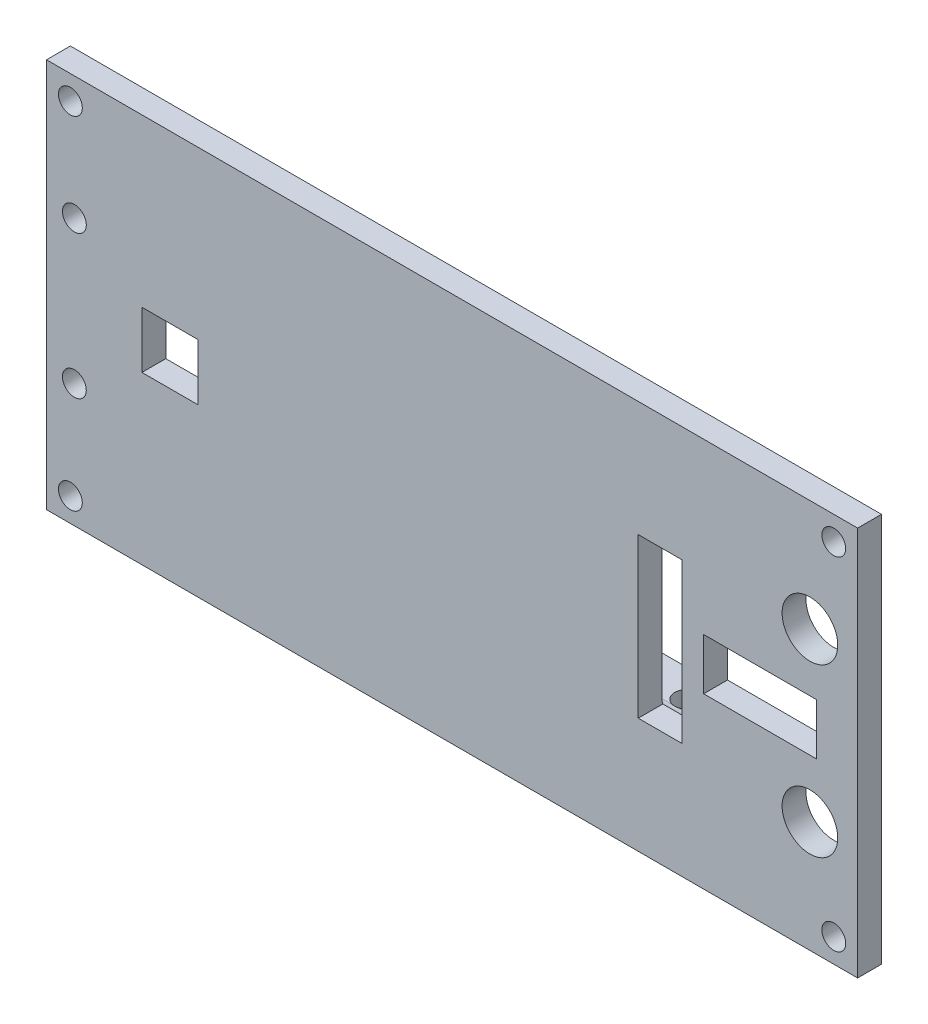
SolidWorks part; units mm, degrees
ref_plane "前视基准面" through (0, 0, 0) normal (0, 0, 1) x (1, 0, 0)
ref_plane "上视基准面" through (0, 0, 0) normal (0, 1, 0) x (1, 0, 0)
ref_plane "右视基准面" through (0, 0, 0) normal (1, 0, 0) x (0, 0, -1)
sketch "草图1" plane through (0, 0, 0) normal (0, 0, 1) x (1, 0, 0)
  line L1 (31, 0) -> (133, 0)
  line L2 (31, 0) -> (31, -49)
  line L3 (31, -49) -> (133, -49)
  line L4 (133, 0) -> (133, -49)
  dimension "D1" = 102
  dimension "D2" = 49
extrude "凸台-拉伸1" add sketch "草图1" along normal blind 3
sketch "草图2" plane through (0, 0, 0) normal (0, 0, -1) x (-1, 0, 0)
  line L1 (-31, 0) -> (-31, -49) construction
  line L2 (-133, -49) -> (-133, 0) construction
  line L3 (-133, 0) -> (-31, 0) construction
  line L4 (-31, -24.5) -> (-14.5, -24.5) construction
  line L9 (-14.5, -24.5) -> (-130, -24.5) construction
  line L10 (-130, -24.5) -> (-130, -46) construction
  line L12 (-34.5, -15.5) -> (-34.5, -33.5) construction
  line L13 (-130, -3) -> (-34, -3) construction
  circle A6 centre (-130, -46) radius 1.5
  circle A7 centre (-130, -3) radius 1.5
  circle A8 centre (-34, -3) radius 1.5
  circle A9 centre (-34.5, -15.5) radius 1.5
  circle A11 centre (-34, -46) radius 1.5
  circle A12 centre (-34.5, -33.5) radius 1.5
  dimension "D4" = 21.5
  dimension "D2" = 3
  dimension "D7" = 3
  dimension "D1" = 96
  dimension "D3" = 3
  dimension "D9" = 18
extrude "切除-拉伸1" cut sketch "草图2" against normal through all
sketch "草图3" plane through (0, 0, 0) normal (0, 0, -1) x (-1, 0, 0)
  line L0 (-133, -24.5) -> (-83, -24.5) construction
  line L1 (-133, -49) -> (-133, 0) construction
  line L2 (-83, -24.5) -> (-83.2346, -13.1) construction
  line L3 (-83.2346, -43.5) -> (-83.2346, -1.5) construction
  line L4 (-83.2346, -13.1) -> (-49, -13.1) construction
  line L6 (-49, -13.1) -> (-111, -13.1)
  line L7 (-49, -13.1) -> (-49, -10.1)
  line L8 (-49, -10.1) -> (-111, -10.1)
  line L9 (-111, -13.1) -> (-111, -10.1)
  line L10 (-31, 0) -> (-31, -49) construction
  line L11 (-49, -35.9) -> (-49, -38.9)
  line L12 (-49, -38.9) -> (-111, -38.9)
  line L13 (-111, -35.9) -> (-111, -38.9)
  line L14 (-49, -35.9) -> (-111, -35.9)
  dimension "D1" = 11.4
  dimension "D2" = 3
  dimension "D3" = 22
  dimension "D4" = 18
extrude "凸台-拉伸2" add sketch "草图3" along normal blind 7
fillet "圆角1" radius 2 1 edges at (80, -13.1, 0)
fillet "圆角2" radius 2 1 edges at (80, -35.9, 0)
hole_wizard "大小mm Press 暗销孔1" positions "草图4" profile "草图5" hole size "Ø3.0" standard "ISO" end condition through all
sketch "草图4" plane through (43.0008, -10.1, 120.3028) normal (0, 1, 0) x (0.9998, 0, -0.021)
  point P0 (20.5912, 123.3982)
  point P2 (42.5912, 122.9368)
  point P4 (64.5816, 122.4756)
sketch "草图5" plane through (61, -10.1, -3.5) normal (1, 0, 0) x (0, 0, 1)
  line L0 (0, 0) -> (0, 38.9)
  line L1 (0, 38.9) -> (1.5, 38.9)
  line L2 (1.5, 38.9) -> (1.5, 0)
  line L3 (1.5, 0) -> (0, 0)
  line L4 (0, -6.35) -> (0, 107.95) construction
  dimension "通孔孔直径" = 3
  dimension "通孔孔深度" = 38.9
sketch "草图6" plane through (0, 0, 3) normal (0, 0, 1) x (1, 0, 0)
  line L0 (110.9096, -24.5) -> (134.0566, -24.5) construction
  line L1 (110.9096, -34.5) -> (105.4096, -34.5)
  line L2 (110.9096, -34.5) -> (110.9096, -14.5)
  line L3 (110.9096, -14.5) -> (105.4096, -14.5)
  line L4 (105.4096, -34.5) -> (105.4096, -14.5)
  line L5 (50.0504, -28.0495) -> (43.0008, -28.0495)
  line L6 (50.0504, -28.0495) -> (50.0504, -20.9505)
  line L7 (50.0504, -20.9505) -> (43.0008, -20.9505)
  line L8 (43.0008, -28.0495) -> (43.0008, -20.9505)
  line L9 (133, -24.5) -> (125.2622, -24.5) construction
  line L10 (133, -49) -> (133, 0) construction
  line L11 (50.0504, -24.5) -> (56.2504, -24.5) construction
  line L12 (133, 0) -> (31, 0) construction
  line L14 (127.831, -21.2717) -> (113.6365, -21.2717)
  line L15 (127.831, -21.2717) -> (127.831, -27.7283)
  line L16 (127.831, -27.7283) -> (113.6365, -27.7283)
  line L17 (113.6365, -21.2717) -> (113.6365, -27.7283)
  line L18 (127.831, -21.2717) -> (113.6365, -27.7283) construction
  line L19 (127.831, -27.7283) -> (113.6365, -21.2717) construction
  circle A0 centre (127, -14) radius 3.5
  circle A2 centre (127, -35) radius 3.5
  point P8 (0, 0)
  point P23 (120.7337, -24.5)
  dimension "D4" = 7
  dimension "D5" = 6
  dimension "D6" = 10.5
  dimension "D1" = 5.5
  dimension "D2" = 20
  dimension "D3" = 14
extrude "切除-拉伸2" cut sketch "草图6" against normal blind 7
